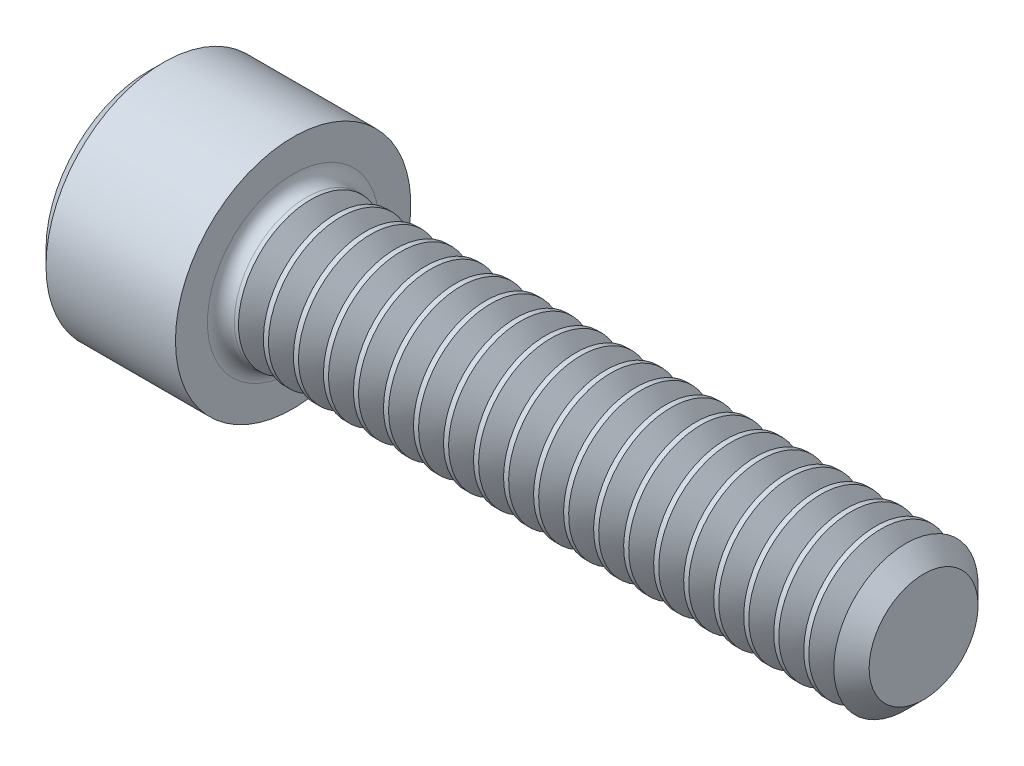
SolidWorks part; units mm, degrees
ref_plane "Plane1" through (0, 0, 0) normal (0, 0, 1) x (1, 0, 0)
ref_plane "Plane2" through (0, 0, 0) normal (0, 1, 0) x (1, 0, 0)
ref_plane "Plane3" through (0, 0, 0) normal (1, 0, 0) x (0, 0, -1)
sketch "BodySke" plane through (0, 0, 0) normal (0, 0, 1) x (1, 0, 0)
  line L0 (0, 0) -> (0, 1.5494)
  line L1 (0.2286, 1.778) -> (2.1844, 1.778)
  line L2 (2.1844, 1.778) -> (2.1844, 1.0922)
  line L3 (2.1844, 1.0922) -> (11.4402, 1.0922)
  line L4 (11.7094, 0.823) -> (11.7094, 0)
  line L5 (11.7094, 0) -> (0, 0)
  line L6 (-31.75, 0) -> (127, 0) construction
  line L7 (0, 1.5494) -> (0.2286, 1.778)
  line L8 (11.7094, 0.823) -> (11.4402, 1.0922)
  line L9 (0, -1.5494) -> (0.2286, -1.778) construction
  line L10 (11.7094, -0.823) -> (11.4402, -1.0922) construction
  line L11 (2.6391, 9.525) -> (2.6391, 3.175) construction
  line L12 (2.1844, 9.525) -> (2.1844, 3.175) construction
  line L13 (-26.3906, 9.525) -> (-26.3906, 3.175) construction
  dimension "Diameter" = 2.1844
  dimension "Head_ht" = 2.1844
  dimension "Length" = 9.525
  dimension "Body_ch_ang" = 45
  dimension "Head_dia" = 3.556
  dimension "Head_ch_ang" = 45
  dimension "Head_side_ht" = 1.9558
  dimension "Minor_dia" = 1.6459
  dimension "Advance" = 0.4547
  dimension "Thread_nom" = 9.525
  dimension "Thread_length" = 38.1
revolve "Base-Revolve" add sketch "BodySke"
cosmetic thread "ThreadCosmetic" [suppressed]
fillet "Fillet1" radius 0.2032 1 edges at (2.1844, 0, 1.0922)
sketch "Sketch2" plane through (0, 0, 0) normal (0, 0, 1) x (1, 0, 0)
  line L0 (0, 0.9906) -> (0.9652, 0.9906)
  line L1 (0.9652, 0.9906) -> (1.5371, 0)
  line L2 (-31.75, 0) -> (127, 0) construction
  line L3 (1.5371, 0) -> (0, 0)
  line L4 (0, 0) -> (0, 0.9906)
  line L5 (0, 1.5494) -> (0, -1.5494) construction
  line L6 (0, 0) -> (47.625, 0) construction
  line L7 (2.1844, -1.778) -> (2.1844, 1.778) construction
  dimension "D1" = 0.9906
  dimension "D2" = 60
  dimension "Wall_thickness" = 1.2192
revolve "Hex-PreBroach" cut sketch "Sketch2" angle 360 about L6
sketch "Sketch3" plane through (0, 0, 0) normal (-1, 0, 0) x (0, 0.5, 0.866)
  line L0 (0.5719, 0.9906) -> (-0.5719, 0.9906)
  line L1 (-0.5719, 0.9906) -> (-1.1438, 0)
  line L2 (0.5719, 0.9906) -> (1.1438, 0)
  line L3 (0.5719, -0.9906) -> (1.1438, 0)
  line L4 (0.5719, -0.9906) -> (-0.5719, -0.9906)
  line L5 (-0.5719, -0.9906) -> (-1.1438, 0)
  dimension "D1" = 0.9906
  dimension "D2" = 0.9906
  dimension "Hex_size" = 1.9812
extrude "Hex" cut sketch "Sketch3" against normal blind 0.9652
sketch "Sketch4" plane through (0, 0, 0) normal (-1, 0, 0) x (0, 0, 1)
  line L0 (0, 0) -> (1.2446, 0)
  line L1 (0, 0) -> (6.1484, 3.5498) construction
  line L2 (0, 0) -> (0.6223, 1.0779)
  line L3 (1.0085, 0.2596) -> (1.19, 0.3644)
  line L4 (0.7291, 0.7436) -> (0.9106, 0.8484)
  arc A0 (1.0085, 0.2596) -> (0.7291, 0.7436) centre (0, 0) ccw
  arc A1 (1.2446, 0) -> (1.19, 0.3644) centre (0, 0) ccw
  arc A2 (0.6223, 1.0779) -> (0.9106, 0.8484) centre (0, 0) cw
  dimension "D1" = 30
  dimension "Spline_n_dim" = 2.0828
  dimension "Spline_m_dim" = 2.4892
  dimension "D2" = 60
  dimension "D3" = 0.2794
  dimension "Spline_p_dim" = 0.5588
extrude "Spline" [suppressed] cut sketch "Sketch4" against normal blind 0.9652
pattern_circular "CirPattern1" [suppressed] count 6 every 60
sketch "Sketch5" plane through (0, 0, 0) normal (0, 0, 1) x (1, 0, 0)
  line L0 (-31.75, 0) -> (127, 0) construction
  line L2 (0, 1.5494) -> (0, -1.5494) construction
  circle A0 centre (0.254, 0) radius 0.0127
  dimension "Drilled_hole_dia" = 0.0254
  dimension "Drilled_hole_loc" = 0.254
extrude "Hole" [suppressed] cut sketch "Sketch5" against normal through all and the other way through all
pattern_circular "Drilled-4" [suppressed] count 2 every 60
pattern_circular "Drilled-6" [suppressed] count 3 every 60
sketch "ThdSchSke" plane through (0, 0, 0) normal (0, 0, 1) x (1, 0, 0)
  line L0 (2.6391, -0.823) -> (2.4505, -1.0922)
  line L1 (2.6391, -0.823) -> (2.8276, -1.0922)
  line L2 (2.8276, -1.0922) -> (2.8276, -1.3653)
  line L3 (-3.175, 0) -> (5.1513, 0) construction
  line L5 (2.8276, -1.3653) -> (2.4505, -1.3653)
  line L6 (2.4505, -1.3653) -> (2.4505, -1.0922)
  line L7 (0, 1.5494) -> (0, -1.5494) construction
  dimension "Thread_minor" = 1.6459
  dimension "Diameter" = 2.1844
  dimension "Start" = 2.6391
  dimension "SideAngle" = 55
  dimension "VeeAngle" = 70
  dimension "Overcut" = 2.7305
revolve "ThreadSchematic" cut sketch "ThdSchSke" angle 360 about L3
pattern_linear "ThdSchPat" count 20 spacing 0.4535 along (1, 0, 0) of "ThreadSchematic"
equation "\"D2@Sketch3\" = \"Hex_size@Sketch3\" / 2"
equation "\"D1@Sketch3\" = \"Hex_size@Sketch3\" / 2"
equation "\"D1@Sketch2\" = \"Hex_size@Sketch3\" / 2"
equation "\"D3@Sketch4\" = \"Spline_p_dim@Sketch4\" / 2"
equation "\"Thread_minor@ThreadCosmetic\"  =  \"Minor_dia@BodySke\""
equation "\"D2@CirPattern1\" = 360 / \"Num_teeth@CirPattern1\""
equation "\"Wall_thickness@Sketch2\" = \"Head_ht@BodySke\" - \"Key_eng@Hex\""
equation "\"Thread_length@ThreadCosmetic\" = ((sgn( (\"Length@BodySke\" - \"Advance@BodySke\" ) - \"Thread_nom@BodySke\" )-1)*( (\"Length@BodySke\" - \"Advance@BodySke\" ) - \"Thread_nom@BodySke\" ))/-2+ \"Thread_nom@BodySke\""
equation "\"Thread_minor@ThdSchSke\" = \"Minor_dia@BodySke\""
equation "\"Diameter@ThdSchSke\" = \"Diameter@BodySke\""
equation "\"Overcut@ThdSchSke\" = \"Diameter@BodySke\" * 1.25"
equation "\"Start@ThdSchSke\" = \"Head_ht@BodySke\" + \"Length@BodySke\" - \"Thread_length@ThreadCosmetic\"  '---Non-countersunk---"
equation "\"Num_threads@ThdSchPat\" = int( \"Thread_length@ThreadCosmetic\" / \"Advance@BodySke\" + 0.999 )  + 1"
equation "\"Advance@ThdSchPat\" = \"Thread_length@ThreadCosmetic\" /  (\"Num_threads@ThdSchPat\" - 1) 'relax it"
equation "\"Num_threads@ThdSchPat\" = \"Num_threads@ThdSchPat\" - sgn( \"Num_threads@ThdSchPat\" - 1) '---chamfered tips only---"
